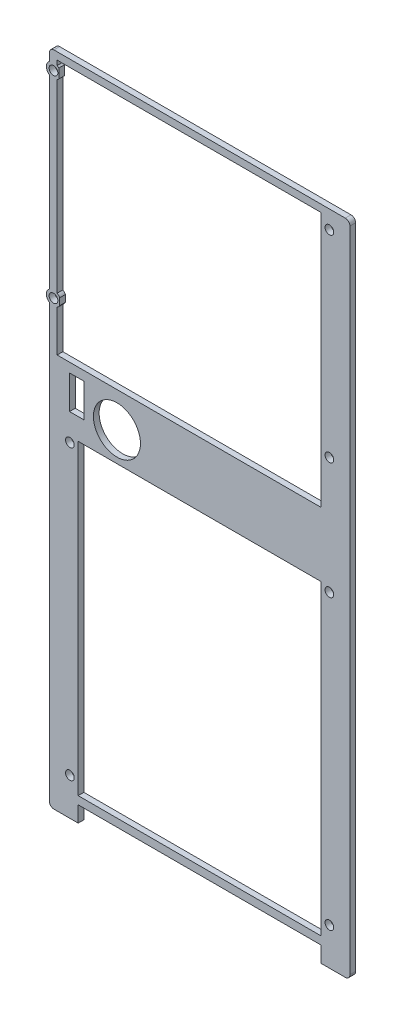
SolidWorks part; units mm, degrees
ref_plane "Front" through (0, 0, 0) normal (0, 0, 1) x (1, 0, 0)
ref_plane "Top" through (0, 0, 0) normal (0, 1, 0) x (1, 0, 0)
ref_plane "Right" through (0, 0, 0) normal (1, 0, 0) x (0, 0, -1)
sketch "Sketch1" plane through (0, 0, 0) normal (0, 0, 1) x (1, 0, 0)
  line L0 (0, 0) -> (0, 108.7427) construction
  line L1 (67.448, 180.1584) -> (67.448, 38.3743)
  line L4 (67.448, -180.8708) -> (80.8753, -180.8708)
  line L5 (-67.448, -180.8708) -> (-80.8753, -180.8708)
  line L6 (83.4153, -178.3308) -> (83.4153, 181.6344)
  line L7 (-83.4153, -178.3308) -> (-83.4153, 61.4863)
  line L8 (80.8753, 184.1744) -> (67.448, 184.1744)
  line L9 (-80.8753, 184.1744) -> (67.448, 184.1744)
  line L10 (-67.448, -172.0613) -> (-67.448, -180.8708)
  line L11 (67.448, 180.1584) -> (-79.1185, 180.1584)
  line L12 (-67.448, 2.7053) -> (-67.448, -167.6565)
  line L13 (-83.4153, 177.3787) -> (-83.4153, 181.6344)
  line L14 (-79.1185, 180.1584) -> (-79.1185, 177.5312)
  line L15 (67.448, -167.6565) -> (-67.448, -167.6565)
  line L16 (-64.1243, 33.2068) -> (-72.2262, 33.2068)
  line L17 (67.448, -172.0613) -> (-67.448, -172.0613)
  line L18 (-79.1185, 38.3743) -> (67.448, 38.3743)
  line L19 (67.448, 2.7053) -> (67.448, -167.6565)
  line L20 (67.448, -172.0613) -> (67.448, -180.8708)
  line L21 (-67.448, 2.7053) -> (67.448, 2.7053)
  line L22 (-64.1243, 33.2068) -> (-64.1243, 14.62)
  line L23 (-64.1243, 14.62) -> (-72.2262, 14.62)
  line L24 (-72.2262, 33.2068) -> (-72.2262, 14.62)
  line L25 (-79.1185, 170.7863) -> (-79.1185, 68.0787)
  line L26 (-78.2077, 176.7748) -> (-78.2077, 171.5427)
  line L27 (-83.4153, 67.9262) -> (-83.4153, 170.9388)
  line L28 (-79.1185, 61.3338) -> (-79.1185, 38.3743)
  line L29 (-77.6964, 66.5965) -> (-77.6964, 62.816)
  arc A0 (83.4153, 181.6344) -> (80.8753, 184.1744) centre (80.8753, 181.6344) ccw
  arc A1 (-83.4153, 181.6344) -> (-80.8753, 184.1744) centre (-80.8753, 181.6344) cw
  arc A2 (-80.8753, -180.8708) -> (-83.4153, -178.3308) centre (-80.8753, -178.3308) cw
  arc A3 (80.8753, -180.8708) -> (83.4153, -178.3308) centre (80.8753, -178.3308) ccw
  circle A5 centre (-81.1499, 174.1587) radius 2.413 construction
  circle A6 centre (-45.925, 18.948) radius 13.062
  circle A7 centre (-45.925, 18.948) radius 13.062
  circle A8 centre (-72.0334, -0.1046) radius 2.413 construction
  circle A9 centre (-72.0334, -160.14) radius 2.413 construction
  circle A10 centre (72.0334, -160.14) radius 2.413 construction
  circle A11 centre (72.0334, 174.1587) radius 2.413 construction
  circle A12 centre (72.0334, 64.7063) radius 2.413 construction
  circle A13 centre (72.0334, -0.1046) radius 2.413 construction
  circle A14 centre (-81.1499, 174.1587) radius 2.413
  circle A15 centre (-72.0334, -0.1046) radius 2.413
  circle A16 centre (-72.0334, -160.14) radius 2.413
  circle A17 centre (72.0334, -160.14) radius 2.413
  circle A18 centre (72.0334, 174.1587) radius 2.413
  circle A19 centre (72.0334, 64.7063) radius 2.413
  circle A20 centre (72.0334, -0.1046) radius 2.413
  arc A22 (-79.1185, 170.7863) -> (-78.2077, 171.5427) centre (-81.1499, 174.1587) ccw
  arc A23 (-83.4153, 177.3787) -> (-83.4153, 170.9388) centre (-81.1499, 174.1587) ccw
  arc A24 (-78.2077, 176.7748) -> (-79.1185, 177.5312) centre (-81.1499, 174.1587) ccw
  arc A25 (-77.6964, 66.5965) -> (-77.6964, 62.816) centre (-81.1499, 64.7063) ccw construction
  arc A26 (-77.6964, 66.5965) -> (-79.1185, 68.0787) centre (-81.1499, 64.7063) ccw
  circle A27 centre (-81.1499, 64.7063) radius 2.413 construction
  circle A28 centre (-81.1499, 64.7063) radius 2.413
  arc A29 (-79.1185, 61.3338) -> (-77.6964, 62.816) centre (-81.1499, 64.7063) ccw
  arc A30 (-83.4153, 67.9262) -> (-83.4153, 61.4863) centre (-81.1499, 64.7063) ccw
  point P13 (83.4153, 184.1744)
  point P16 (-83.4153, 184.1744)
  point P19 (-83.4153, -180.8708)
  point P22 (83.4153, -180.8708)
  dimension "D1" = 2.54
  dimension "D2" = 1.27
extrude "Base-Extrude" add sketch "Sketch1" against normal blind 3.175
